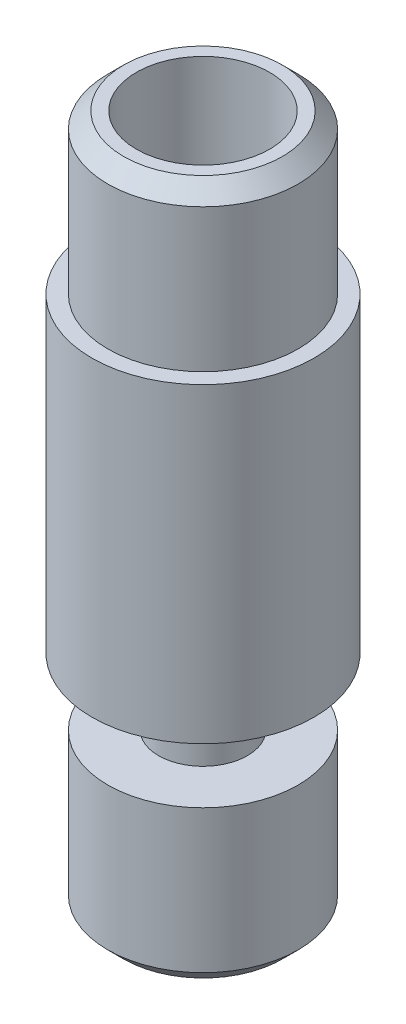
SolidWorks part; units mm, degrees
material "1060 Alloy"
ref_plane "Front Plane" through (0, 0, 0) normal (0, 0, 1) x (1, 0, 0)
ref_plane "Top Plane" through (0, 0, 0) normal (0, 1, 0) x (1, 0, 0)
ref_plane "Right Plane" through (0, 0, 0) normal (1, 0, 0) x (0, 0, -1)
ref_plane "Plane1" through (0, 0, 0) normal (0, 0, -1) x (-1, 0, 0)
sketch "Sketch1" plane through (0, 0, 0) normal (0, 0, -1) x (-1, 0, 0)
  line L0 (-2.5, 0) -> (-1, 0)
  line L1 (-1, 0) -> (-1, 15.8)
  line L2 (-1, 15.8) -> (-2.1, 16.9)
  line L3 (-2.1, 16.9) -> (-2.1, 21.9)
  line L4 (-2.1, 21.9) -> (-2.5, 21.9)
  line L5 (-2.5, 21.9) -> (-3, 21.4)
  line L6 (-3, 21.4) -> (-3, 16.9)
  line L7 (-3, 16.9) -> (-3.5, 16.9)
  line L8 (-3.5, 16.9) -> (-3.5, 7.1)
  line L9 (-3.5, 7.1) -> (-1.4, 7.1)
  line L10 (-1.4, 7.1) -> (-1.4, 5)
  line L11 (-1.4, 5) -> (-3, 5)
  line L12 (-3, 5) -> (-3, 0.5)
  line L13 (-3, 0.5) -> (-2.5, 0)
  line L14 (0, 0) -> (0, 21.9) construction
revolve "Revolve1" add sketch "Sketch1" angle 360 about L14
